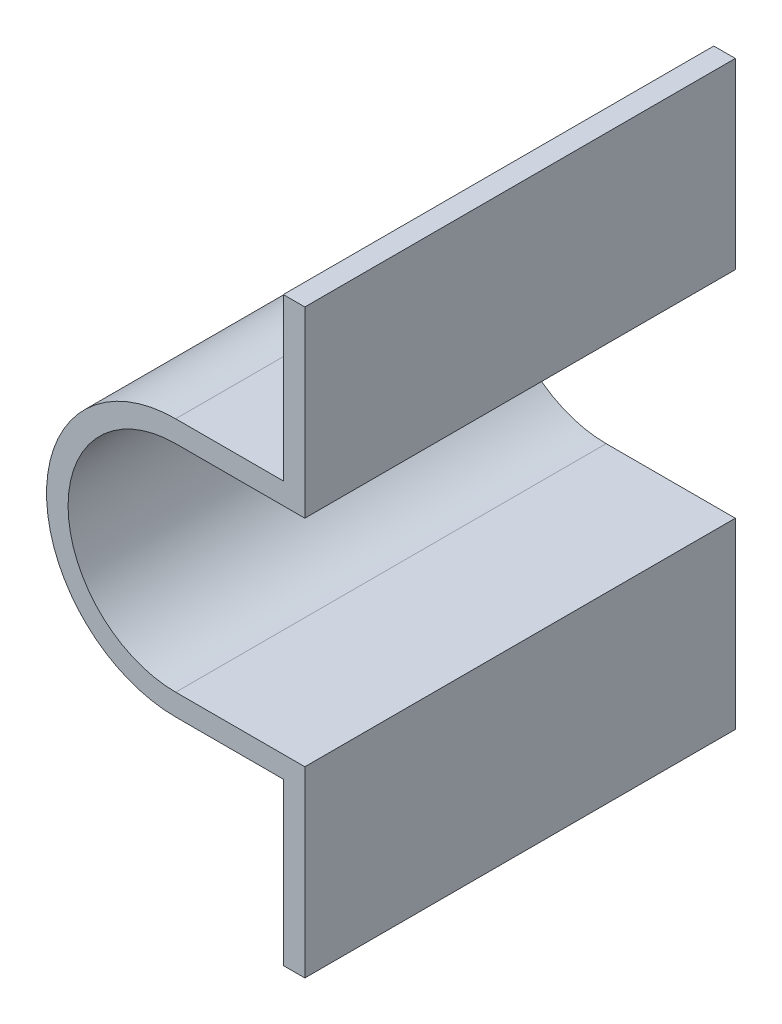
SolidWorks part; units mm, degrees
ref_plane "Front Plane" through (0, 0, 0) normal (0, 0, 1) x (1, 0, 0)
ref_plane "Top Plane" through (0, 0, 0) normal (0, 1, 0) x (1, 0, 0)
ref_plane "Right Plane" through (0, 0, 0) normal (1, 0, 0) x (0, 0, -1)
sketch "Sketch1" plane through (0, 0, 0) normal (0, 0, 1) x (1, 0, 0)
  line L2 (0, 10) -> (0, -10) construction
  line L3 (0, 12) -> (10, 12)
  line L5 (12, 10) -> (0, 10)
  line L6 (0, -10) -> (12, -10)
  line L8 (10, -12) -> (0, -12)
  line L9 (10, 12) -> (10, 27)
  line L10 (10, 27) -> (12, 27)
  line L11 (12, 27) -> (12, 10)
  line L14 (12, -10) -> (12, -27)
  line L15 (12, -27) -> (10, -27)
  line L16 (10, -27) -> (10, -12)
  arc A0 (0, 10) -> (0, -10) centre (0, 0) ccw
  arc A1 (0, 12) -> (0, -12) centre (0, 0) ccw
  dimension "D1" = 10
  dimension "D2" = 2
  dimension "D3" = 10
  dimension "D4" = 15
  dimension "D5" = 2
extrude "Boss-Extrude1" add sketch "Sketch1" along normal blind 40
